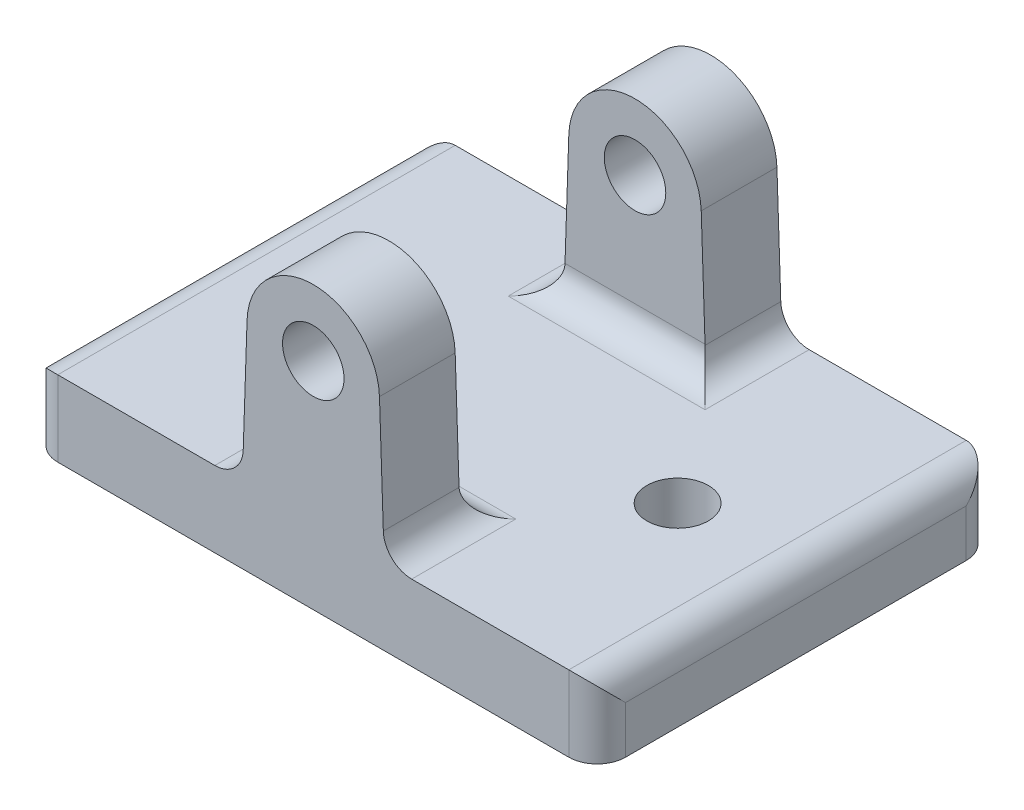
SolidWorks part; units mm, degrees
material "ABS"
ref_plane "Front Plane" through (0, 0, 0) normal (0, 0, 1) x (1, 0, 0)
ref_plane "Top Plane" through (0, 0, 0) normal (0, 1, 0) x (1, 0, 0)
ref_plane "Right Plane" through (0, 0, 0) normal (1, 0, 0) x (0, 0, -1)
sketch "Sketch2" plane through (0, 0, 0) normal (0, 1, 0) x (1, 0, 0)
  line L0 (-17.5, 0) -> (0, 0) construction
  line L1 (-30, -21) -> (30, -21)
  line L2 (-30, -21) -> (-30, 21)
  line L3 (-30, 21) -> (30, 21)
  line L4 (30, -21) -> (30, 21)
  line L5 (-30, -21) -> (30, 21) construction
  line L6 (-30, 21) -> (30, -21) construction
  line L7 (0, -55) -> (0, 55) construction
  circle A0 centre (-17.5, 0) radius 3.25
  circle A1 centre (17.5, 0) radius 3.25
  point P0 (0, 0)
  dimension "D4" = 6.5
  dimension "D1" = 42
  dimension "D2" = 60
  dimension "D3" = 17.5
extrude "Boss-Extrude1" add sketch "Sketch2" along normal blind 8
sketch "Sketch3" plane through (0, 0, 21) normal (0, 0, 1) x (1, 0, 0)
  line L0 (-7.5, 8) -> (-6.9961, 23)
  line L1 (-30, 8) -> (30, 8) construction
  line L2 (6.9961, 23) -> (7.5, 8)
  line L3 (-7.5, 8) -> (7.5, 8)
  arc A0 (-6.9961, 23) -> (6.9961, 23) centre (0, 22.765) cw
  circle A1 centre (0, 22.765) radius 3.25
  dimension "D1" = 7
  dimension "D4" = 6.5
  dimension "D2" = 15
  dimension "D3" = 15
extrude "Boss-Extrude2" add sketch "Sketch3" against normal blind 8
mirror "Mirror1" about plane through (0, 0, 0) normal (0, 0, 1) of "Boss-Extrude2"
fillet "Fillet1" radius 3 12 edges at (7.5, 8, -17) (7.5, 8, 17) (-7.5, 8, 17) (-7.5, 8, -17) (30, 8, 0) (0, 8, 13) (-30, 8, 0) (0, 8, -13) (30, 4, 21) (-30, 4, 21) (-30, 4, -21) (30, 4, -21)
